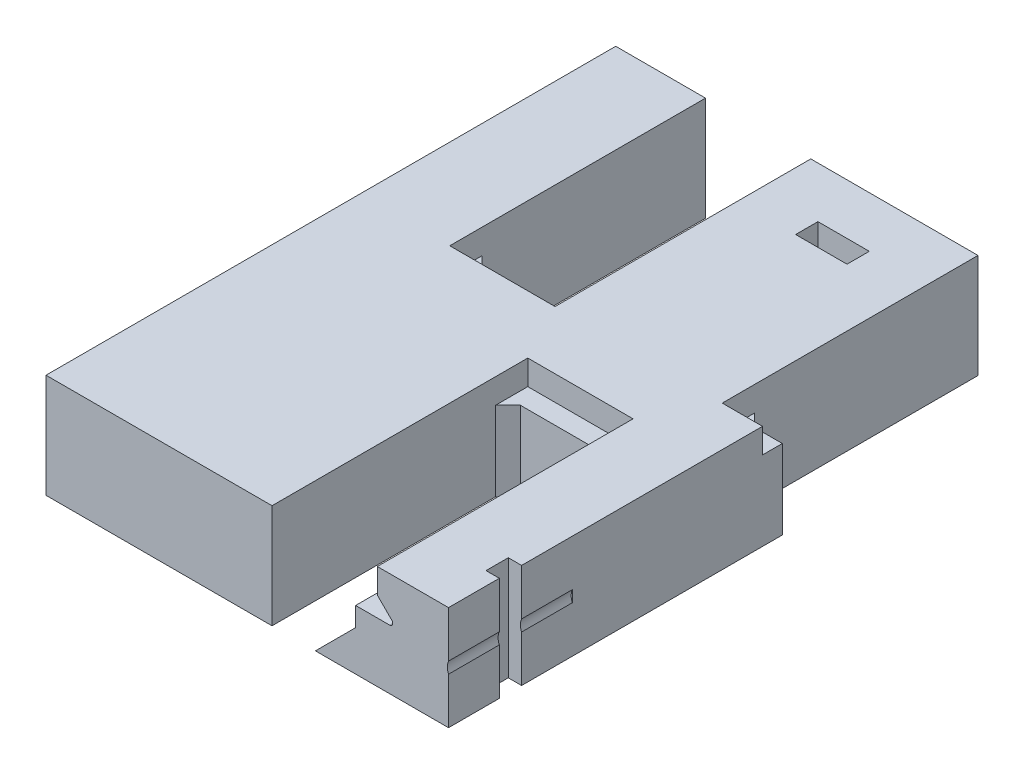
SolidWorks part; units mm, degrees
ref_plane "Front Plane" through (0, 0, 0) normal (0, 0, 1) x (1, 0, 0)
ref_plane "Top Plane" through (0, 0, 0) normal (0, 1, 0) x (1, 0, 0)
ref_plane "Right Plane" through (0, 0, 0) normal (1, 0, 0) x (0, 0, -1)
sketch "Sketch1" plane through (0, 0, 0) normal (0, 1, 0) x (1, 0, 0)
  line L0 (-39, 23) -> (39, -23) construction
  line L1 (-39, 23) -> (39, 23)
  line L2 (-39, 23) -> (-39, -23)
  line L3 (-39, -23) -> (39, -23)
  line L4 (39, 23) -> (39, -23)
  dimension "D1" = 78
  dimension "D2" = 46
extrude "Boss-Extrude1" add sketch "Sketch1" along normal mid plane 8.4
sketch "Sketch2" plane through (0, 0, -23) normal (0, 0, -1) x (-1, 0, 0)
  line L0 (-39, 4.2) -> (39, 4.2) construction
  line L1 (-31.75, 4.2) -> (-23.25, 4.2)
  line L2 (-31.75, 4.2) -> (-31.75, 2.2)
  line L3 (-31.75, 2.2) -> (-23.25, 2.2)
  line L4 (-23.25, 4.2) -> (-23.25, 2.2)
  line L6 (-39, 4.2) -> (-39, -4.2) construction
  line L7 (-39, -4.2) -> (39, -4.2) construction
  dimension "D1" = 8.5
  dimension "D2" = 7.25
  dimension "D3" = 6.4
extrude "Cut-Extrude1" cut sketch "Sketch2" against normal blind 20.65
sketch "Sketch3" plane through (0, 2.2, 0) normal (0, 1, 0) x (1, 0, 0)
  line L0 (23.25, 23) -> (23.25, 20.3)
  line L1 (23.25, 20.3) -> (24.25, 21.3)
  line L2 (24.25, 21.3) -> (30, 21.3)
  line L3 (30, 21.3) -> (30, 3.95)
  line L4 (30, 3.95) -> (24.25, 3.95)
  line L5 (24.25, 3.95) -> (23.25, 4.95)
  line L6 (23.25, 4.95) -> (23.25, 2.35)
  line L7 (23.25, 2.35) -> (31.75, 2.35)
  line L8 (31.75, 2.35) -> (31.75, 23)
  line L9 (31.75, 23) -> (23.25, 23)
  line L10 (31.75, 2.35) -> (31.75, 23) construction
  line L11 (31.75, 2.35) -> (23.25, 2.35) construction
  line L12 (23.25, 2.35) -> (23.25, 23) construction
  line L13 (23.25, 20.3) -> (23.25, 4.95)
  line L14 (30, 21.3) -> (30, 23)
  line L15 (31.75, 23) -> (23.25, 23) construction
  line M12 (23.25, 23) -> (23.25, 2.35)
extrude "Cut-Extrude2" cut sketch "Sketch3" against normal through all contours L5 L4 L3 L2 L1 M12 | L2 L14 L9 L1 M12
sketch "Sketch15" plane through (0, 0, 0) normal (0, 0, 1) x (1, 0, 0)
  line L0 (30, -4.2) -> (26.75, -4.2)
  line L1 (30, -4.2) -> (24.25, -4.2) construction
  line L2 (26.75, -4.2) -> (30, -0.95)
  line L3 (30, -4.2) -> (30, 2.2) construction
  line L4 (30, -0.95) -> (30, -4.2)
  dimension "D1" = 3.5
  dimension "D2" = 45
extrude "Boss-Extrude3" add sketch "Sketch15" against normal up to surface (23 mm away) up to face at (33.5833, 0.7333, -23)
pattern_linear "LPattern1" count 6 spacing 11 along (-1, 0, 0) of "Cut-Extrude2", "Cut-Extrude1", "Boss-Extrude3"
mirror "Mirror3" about plane through (0, 0, 0) normal (0, 0, 1) of "LPattern1", "Cut-Extrude1", "Cut-Extrude2", "Boss-Extrude3"
sketch "Sketch6" plane through (0, 4.2, 0) normal (0, 1, 0) x (1, 0, 0)
  line L1 (-20.75, 23) -> (-12.25, 23)
  line L2 (-20.75, 23) -> (-20.75, 2.35)
  line L3 (-20.75, 2.35) -> (-12.25, 2.35)
  line L4 (-12.25, 23) -> (-12.25, 2.35)
  line L5 (1.25, 23) -> (9.75, 23)
  line L6 (1.25, 23) -> (1.25, 2.35)
  line L7 (1.25, 2.35) -> (9.75, 2.35)
  line L8 (9.75, 23) -> (9.75, 2.35)
  line L9 (23.25, 23) -> (31.75, 23)
  line L10 (23.25, 23) -> (23.25, 2.35)
  line L11 (23.25, 2.35) -> (31.75, 2.35)
  line L12 (31.75, 23) -> (31.75, 2.35)
  line L13 (-31.75, -2.35) -> (-23.25, -2.35)
  line L14 (-31.75, -2.35) -> (-31.75, -23)
  line L15 (-31.75, -23) -> (-23.25, -23)
  line L16 (-23.25, -2.35) -> (-23.25, -23)
  line L17 (-9.75, -2.35) -> (-1.25, -2.35)
  line L18 (-9.75, -2.35) -> (-9.75, -23)
  line L19 (-9.75, -23) -> (-1.25, -23)
  line L20 (-1.25, -2.35) -> (-1.25, -23)
  line L21 (12.25, -2.35) -> (20.75, -2.35)
  line L22 (12.25, -2.35) -> (12.25, -23)
  line L23 (12.25, -23) -> (20.75, -23)
  line L24 (20.75, -2.35) -> (20.75, -23)
extrude "Boss-Extrude2" add sketch "Sketch6" against normal up to surface (8.4 mm away) up to face at (-2.4844, -4.2, 0)
sketch "Sketch4" plane through (-39, 0, 0) normal (-1, 0, 0) x (0, 0, 1)
  line L0 (-20, -2.2) -> (20, -2.2)
  circle A0 centre (-20, -2.2) radius 1.5
  circle A1 centre (20, -2.2) radius 1.5
  dimension "D1" = 3
  dimension "D2" = 40
  dimension "D3" = 2.2
extrude "Cut-Extrude3" cut sketch "Sketch4" along direction (-1, 0, 0) on the side against the normal blind 5
mirror "Mirror1" about plane through (0, 0, 0) normal (1, 0, 0) of "Cut-Extrude3"
sketch "Sketch7" plane through (0, 0, 23) normal (0, 0, 1) x (1, 0, 0)
  line L0 (1.25, -4.2) -> (1.25, 2.2) construction
  line L2 (23.25, 2.2) -> (23.25, 4.2) construction
  circle A0 centre (-5.5, 0) radius 1.1
  circle A1 centre (16.5, 0) radius 1.1
  dimension "D1" = 2.2
  dimension "D2" = 6.75
  dimension "D3" = 6.75
extrude "Cut-Extrude4" cut sketch "Sketch7" against normal blind 10
sketch "Sketch9" plane through (0, 4.2, 0) normal (0, 1, 0) x (1, 0, 0)
  line L0 (-7.575, -17.1) -> (-3.425, -18.9) construction
  line L1 (-7.575, -17.1) -> (-3.425, -17.1)
  line L2 (-7.575, -17.1) -> (-7.575, -18.9)
  line L3 (-7.575, -18.9) -> (-3.425, -18.9)
  line L4 (-3.425, -17.1) -> (-3.425, -18.9)
  line L5 (14.425, -17.1) -> (18.575, -17.1)
  line L6 (14.425, -17.1) -> (14.425, -18.9)
  line L7 (14.425, -18.9) -> (18.575, -18.9)
  line L8 (18.575, -17.1) -> (18.575, -18.9)
  line L9 (-12.25, -23) -> (1.25, -23) construction
  line L11 (14.425, -17.1) -> (18.575, -18.9)
  line L12 (23.25, -2.35) -> (23.25, -23) construction
  line L13 (9.75, -23) -> (23.25, -23) construction
  line L14 (1.25, -2.35) -> (1.25, -23) construction
  point P8 (-5.5, -18)
  point P13 (16.5, -18)
  dimension "D1" = 5
  dimension "D2" = 4.15
  dimension "D3" = 6.75
  dimension "D4" = 1.8
  dimension "D5" = 4.15
  dimension "D6" = 1.8
  dimension "D7" = 6.75
  dimension "D8" = 5
extrude "Cut-Extrude5" cut sketch "Sketch9" against normal through all contours L1 L0 L4 | L0 L2 L3 | L11 L6 L7 | L5 L11 L8
sketch "Sketch10" plane through (0, 4.2, 0) normal (0, 1, 0) x (1, 0, 0)
  line L0 (-18.575, 18.9) -> (-14.425, 17.1) construction
  line L1 (-18.575, 18.9) -> (-14.425, 18.9)
  line L2 (-18.575, 18.9) -> (-18.575, 17.1)
  line L3 (-18.575, 17.1) -> (-14.425, 17.1)
  line L4 (-14.425, 18.9) -> (-14.425, 17.1)
  line L5 (-9.75, 23) -> (-23.25, 23) construction
  line L6 (-23.25, 2.35) -> (-23.25, 23) construction
  point P4 (-16.5, 18)
  dimension "D1" = 4.15
  dimension "D2" = 1.8
  dimension "D3" = 5
  dimension "D4" = 6.75
extrude "Cut-Extrude6" cut sketch "Sketch10" against normal through all
sketch "Sketch11" plane through (0, 0, -23) normal (0, 0, -1) x (-1, 0, 0)
  line L0 (9.75, -4.2) -> (9.75, 4.2) construction
  circle A0 centre (16.5, 0) radius 1.1
  dimension "D1" = 2.2
  dimension "D2" = 6.75
extrude "Cut-Extrude7" cut sketch "Sketch11" against normal blind 8
pattern_linear "LPattern2" count 2 spacing 22 along (1, 0, 0) of "Cut-Extrude6", "Cut-Extrude7"
sketch "Sketch12" plane through (0, 0, -23) normal (0, 0, -1) x (-1, 0, 0)
  line L0 (-20.75, 2.2) -> (-22.35, 0.6)
  line L1 (-22.35, 0.6) -> (-19, 0.6)
  line L2 (-19, -0.95) -> (-19, 2.2) construction
  line L3 (-20.75, 2.2) -> (-19, 2.2) construction
  line L4 (-20.75, 2.2) -> (-19, 2.2)
  line L5 (-19, 2.2) -> (-19, 0.6)
  dimension "D1" = 135
  dimension "D2" = 1.6
extrude "Cut-Extrude8" cut sketch "Sketch12" against normal up to surface (19.05 mm away) up to face at (16.05, -0.99, -3.95)
sketch "Sketch13" plane through (0, 0, 23) normal (0, 0, 1) x (1, 0, 0)
  line L0 (31.75, 2.2) -> (33.35, 0.6)
  line L1 (33.35, 0.6) -> (30, 0.6)
  line L2 (30, -0.95) -> (30, 2.2) construction
  line L3 (30, 0.6) -> (30, 2.2)
  line L4 (30, 2.2) -> (31.75, 2.2)
  dimension "D1" = 135
  dimension "D2" = 1.6
extrude "Cut-Extrude9" cut sketch "Sketch13" against normal up to surface (19.05 mm away) up to face at (27.05, -0.99, 3.95)
pattern_linear "LPattern3" count 3 spacing 22 along (-1, 0, 0) of "Cut-Extrude8"
pattern_linear "LPattern4" count 3 spacing 22 along (-1, 0, 0) of "Cut-Extrude9"
fillet "Fillet1" radius 0.25 6 edges at (22.35, 0.6, -13.475) (0.35, 0.6, -13.475) (-21.65, 0.6, -13.475) (33.35, 0.6, 13.475) (11.35, 0.6, 13.475) (-10.65, 0.6, 13.475)
mirror "Mirror4" [suppressed]
delete or keep bodies "Body-Delete/Keep 1" [suppressed] type delete bodies bodies 114
ref_plane "Plane1" through (-6.5, 0, 0) normal (1, 0, 0) x (0, 0, -1)
split "Split1" trim tools "Plane1" bodies to split 119 resulting bodies 121 122
delete or keep bodies "Body-Delete/Keep 2" type delete bodies bodies 121
